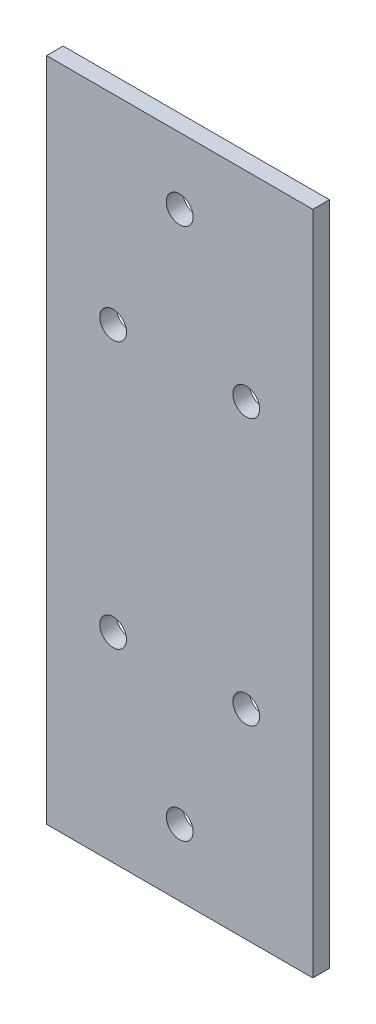
SolidWorks part; units mm, degrees
ref_plane "Front Plane" through (0, 0, 0) normal (0, 0, 1) x (1, 0, 0)
ref_plane "Top Plane" through (0, 0, 0) normal (0, 1, 0) x (1, 0, 0)
ref_plane "Right Plane" through (0, 0, 0) normal (1, 0, 0) x (0, 0, -1)
sketch "Sketch1" plane through (0, 0, 0) normal (0, 0, 1) x (1, 0, 0)
  line L1 (-42.648, 12.1707) -> (8.152, 12.1707)
  line L2 (-42.648, 12.1707) -> (-42.648, -114.8293)
  line L3 (-42.648, -114.8293) -> (8.152, -114.8293)
  line L4 (8.152, 12.1707) -> (8.152, -114.8293)
  circle A0 centre (-17.248, -0.5293) radius 2.5527
  circle A1 centre (-29.948, -25.9293) radius 2.5527
  circle A2 centre (-4.548, -25.9293) radius 2.5527
  circle A3 centre (-17.248, -102.1293) radius 2.5527
  circle A4 centre (-4.548, -76.7293) radius 2.5527
  circle A5 centre (-29.948, -76.7293) radius 2.5527
  dimension "D3" = 5.1054
  dimension "D5" = 38.1
  dimension "D7" = 38.1
  dimension "D1" = 50.8
  dimension "D2" = 127
  dimension "D4" = 12.7
  dimension "D6" = 12.7
  dimension "D8" = 12.7
  dimension "D9" = 38.1
  dimension "D10" = 38.1
  dimension "D11" = 12.7
  dimension "D12" = 12.7
  dimension "D13" = 25.4
extrude "Boss-Extrude1" add sketch "Sketch1" along normal blind 3.175
